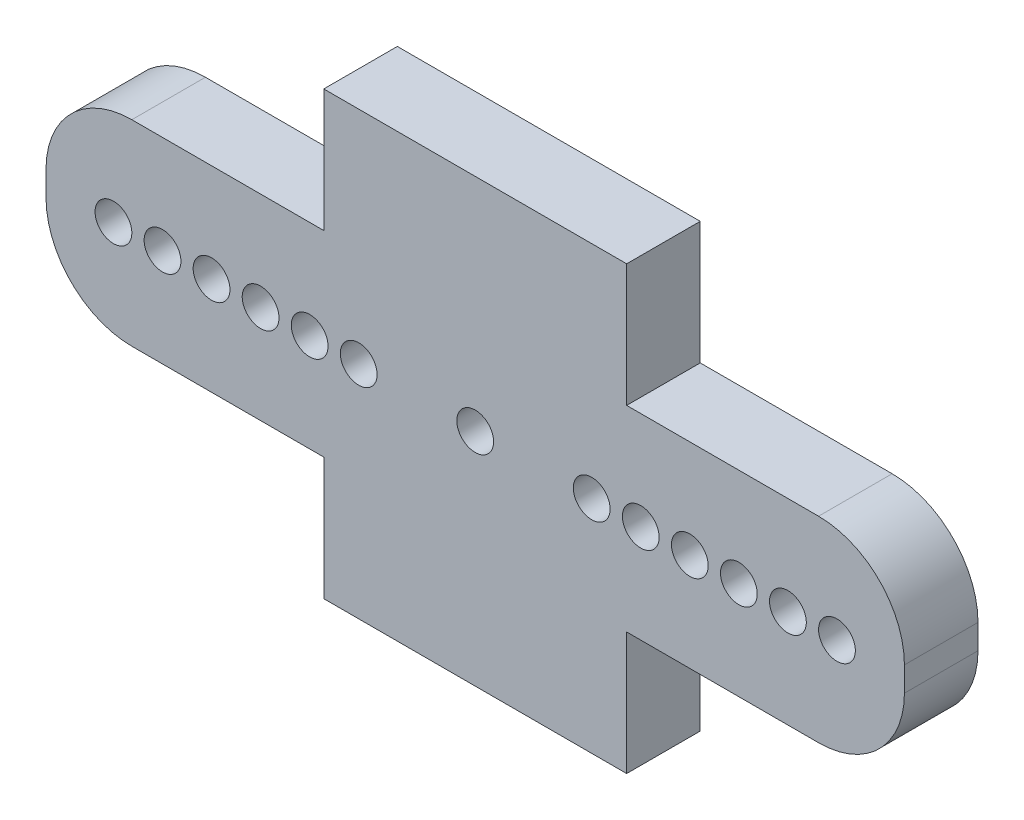
SolidWorks part; units mm, degrees
ref_plane "Front Plane" through (0, 0, 0) normal (0, 0, 1) x (1, 0, 0)
ref_plane "Top Plane" through (0, 0, 0) normal (0, 1, 0) x (1, 0, 0)
ref_plane "Right Plane" through (0, 0, 0) normal (1, 0, 0) x (0, 0, -1)
sketch "Sketch1" plane through (0, 0, 0) normal (0, 0, 1) x (1, 0, 0)
  line L0 (-14, 4) -> (-6.175, 4)
  line L1 (-17.5, 4) -> (17.5, 4) construction
  line L2 (-17.5, 4) -> (-17.5, -4) construction
  line L3 (-17.5, -4) -> (17.5, -4) construction
  line L4 (17.5, 4) -> (17.5, -4) construction
  line L5 (-17.5, 4) -> (17.5, -4) construction
  line L6 (-17.5, -4) -> (17.5, 4) construction
  line L7 (-6.175, 9) -> (6.175, 9) construction
  line L8 (-6.175, 9) -> (-6.175, -9) construction
  line L9 (-6.175, -9) -> (6.175, -9) construction
  line L10 (6.175, 9) -> (6.175, -9) construction
  line L11 (-6.175, 9) -> (6.175, -9) construction
  line L12 (-6.175, -9) -> (6.175, 9) construction
  line L13 (-6.175, 4) -> (-6.175, 9)
  line L14 (-6.175, 9) -> (6.175, 9)
  line L15 (6.175, 9) -> (6.175, 4)
  line L16 (6.175, 4) -> (14, 4)
  line L17 (17.5, 0.5) -> (17.5, -0.5)
  line L18 (14, -4) -> (6.175, -4)
  line L19 (6.175, -4) -> (6.175, -9)
  line L20 (6.175, -9) -> (-6.175, -9)
  line L21 (-6.175, -9) -> (-6.175, -4)
  line L22 (-6.175, -4) -> (-14, -4)
  line L23 (-17.5, -0.5) -> (-17.5, 0.5)
  circle A0 centre (0, 0) radius 0.75
  arc A1 (14, 4) -> (17.5, 0.5) centre (14, 0.5) cw
  arc A2 (17.5, -0.5) -> (14, -4) centre (14, -0.5) cw
  arc A3 (-14, -4) -> (-17.5, -0.5) centre (-14, -0.5) cw
  arc A4 (-14, 4) -> (-17.5, 0.5) centre (-14, 0.5) ccw
  point P0 (0, 0)
  point P6 (0, 0)
  dimension "D5" = 1.5
  dimension "D6" = 3.5
  dimension "D1" = 8
  dimension "D2" = 35
  dimension "D3" = 18
  dimension "D4" = 12.35
extrude "Boss-Extrude1" add sketch "Sketch1" along normal mid plane 3
sketch "Sketch2" plane through (0, 0, 1.5) normal (0, 0, 1) x (1, 0, 0)
  line L0 (-17.5, 0.5) -> (-17.5, -0.5) construction
  circle A0 centre (-14.75, 0) radius 0.75
  circle A1 centre (-12.75, 0) radius 0.75
  circle A2 centre (-10.75, 0) radius 0.75
  circle A3 centre (-8.75, 0) radius 0.75
  circle A4 centre (-6.75, 0) radius 0.75
  circle A5 centre (-4.75, 0) radius 0.75
  dimension "D1" = 1.5
  dimension "D2" = 2.75
  dimension "D4" = 2
  dimension "D3" = 6
extrude "Cut-Extrude1" cut sketch "Sketch2" against normal through all
mirror "Mirror1" about plane through (0, 0, 0) normal (1, 0, 0) of "Cut-Extrude1"
